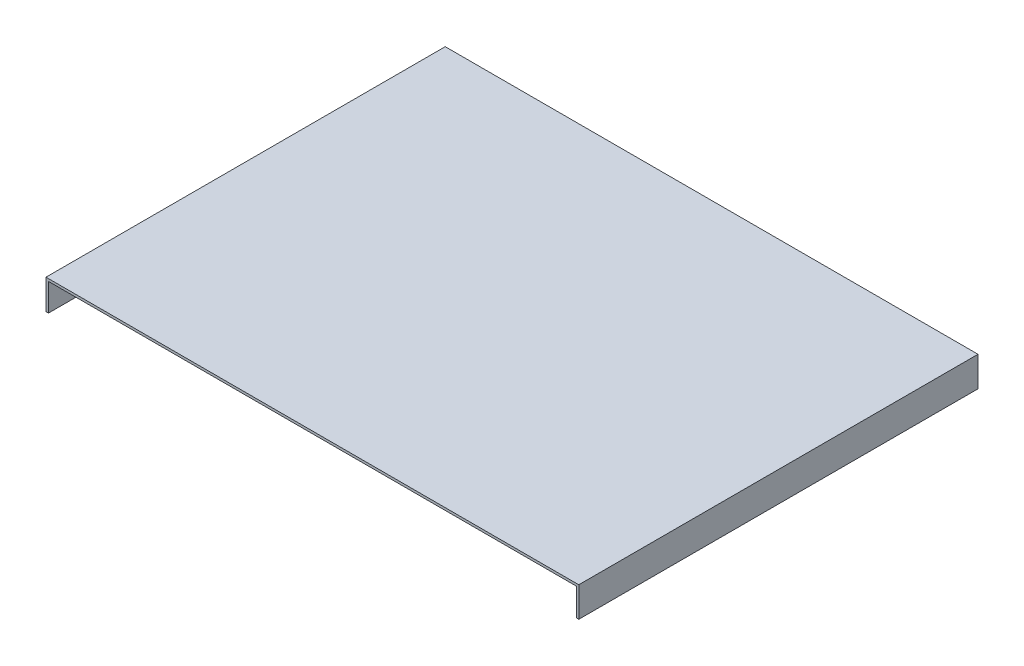
SolidWorks part; units mm, degrees
material "PPS"
ref_plane "Płaszczyzna XY" through (0, 0, 0) normal (0, 0, 1) x (1, 0, 0)
ref_plane "Płaszczyzna XZ" through (0, 0, 0) normal (0, 1, 0) x (1, 0, 0)
ref_plane "Płaszczyzna YZ" through (0, 0, 0) normal (1, 0, 0) x (0, 0, -1)
sketch "Szkic1" plane through (0, 0, 0) normal (0, 0, 1) x (1, 0, 0)
  line L0 (-193.5, 0) -> (193.5, 0)
  line L1 (193.5, 0) -> (193.5, -1.75)
  line L2 (-193.5, 0) -> (-193.5, -1.75)
  line L3 (-193.5, -1.75) -> (193.5, -1.75)
  point P4 (0, 0)
  dimension "D1" = 387
  dimension "D2" = 1.75
  dimension "D3" = 90
  dimension "D4" = 90
extrude "Dodanie-wyciągnięcie1" add sketch "Szkic1" along normal blind 290
sketch "Szkic2" plane through (0, -1.75, 0) normal (0, -1, 0) x (1, 0, 0)
  line L0 (-193.5, 290) -> (-193.5, 0)
  line L1 (-193.5, 0) -> (193.5, 0)
  line L2 (193.5, 0) -> (193.5, 290)
  line L3 (193.5, 290) -> (193.5, 0) construction
  line L4 (193.5, 290) -> (191.75, 290)
  line L5 (-193.5, 290) -> (193.5, 290) construction
  line L6 (191.75, 290) -> (191.75, 1.75)
  line L7 (191.75, 1.75) -> (-191.75, 1.75)
  line L8 (-191.75, 1.75) -> (-191.75, 290)
  line L9 (-191.75, 290) -> (-193.5, 290)
  dimension "D1" = 1.75
  dimension "D2" = 1.75
  dimension "D3" = 1.75
  dimension "D4" = 290
extrude "Dodanie-wyciągnięcie2" add sketch "Szkic2" along normal blind 20
